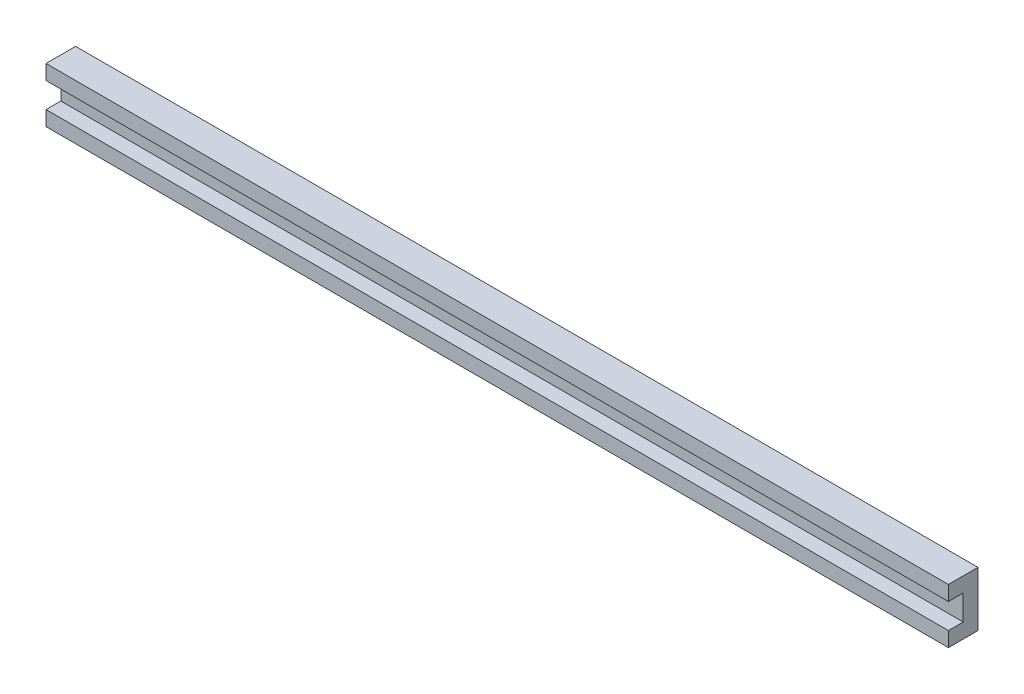
SolidWorks part; units mm, degrees
material "6061-T4 (SS)"
ref_plane "Front Plane" through (0, 0, 0) normal (0, 0, 1) x (1, 0, 0)
ref_plane "Top Plane" through (0, 0, 0) normal (0, 1, 0) x (1, 0, 0)
ref_plane "Right Plane" through (0, 0, 0) normal (1, 0, 0) x (0, 0, -1)
sketch "Sketch1" plane through (0, 0, 0) normal (1, 0, 0) x (0, 0, -1)
  line L0 (0, 0) -> (50.8, 0)
  line L1 (50.8, 0) -> (50.8, 93.98)
  line L2 (50.8, 93.98) -> (0, 93.98)
  line L3 (0, 93.98) -> (0, 68.58)
  line L4 (0, 0) -> (0, 25.4)
  line L5 (0, 25.4) -> (25.4, 25.4)
  line L6 (25.4, 25.4) -> (25.4, 68.58)
  line L7 (25.4, 68.58) -> (0, 68.58)
  dimension "D1" = 93.98
  dimension "D2" = 25.4
  dimension "D3" = 25.4
  dimension "D4" = 50.8
  dimension "D5" = 25.4
extrude "Boss-Extrude1" add sketch "Sketch1" along normal blind 1549.4
